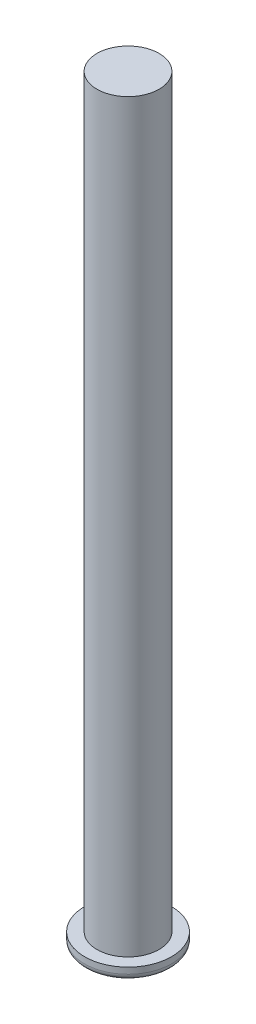
SolidWorks part; units mm, degrees
ref_plane "Front Plane" through (0, 0, 0) normal (0, 0, 1) x (1, 0, 0)
ref_plane "Top Plane" through (0, 0, 0) normal (0, 1, 0) x (1, 0, 0)
ref_plane "Right Plane" through (0, 0, 0) normal (1, 0, 0) x (0, 0, -1)
sketch "Sketch1" plane through (0, 0, 0) normal (0, 1, 0) x (1, 0, 0)
  circle A0 centre (0, 0) radius 5
  dimension "D1" = 10
extrude "Boss-Extrude1" add sketch "Sketch1" along normal blind 120
sketch "Sketch2" plane through (0, 0, 0) normal (0, -1, 0) x (1, 0, 0)
  circle A0 centre (0, 0) radius 7
  circle A1 centre (0, 0) radius 5 construction
  dimension "D1" = 2
extrude "Boss-Extrude2" add sketch "Sketch2" along normal blind 2
fillet "Fillet1" radius 1 1 edges at (0, -2, -7)
